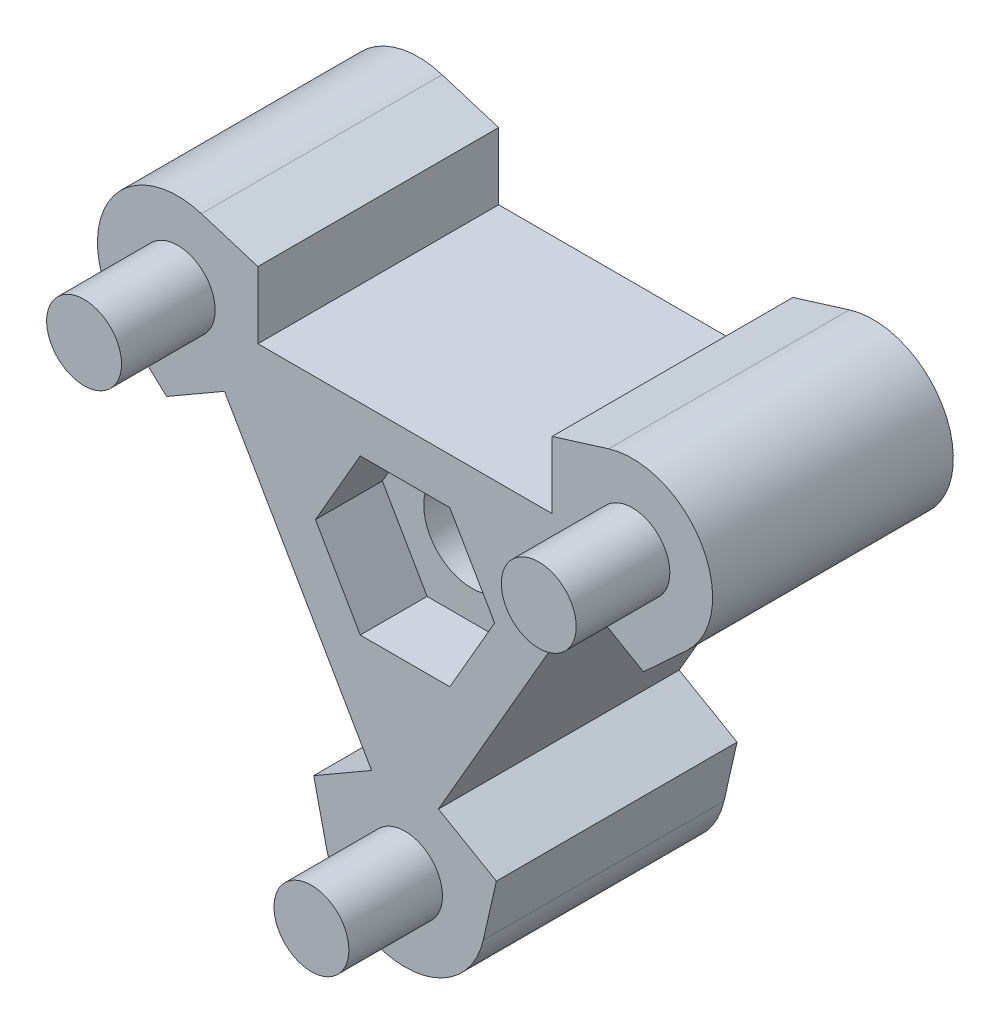
SolidWorks part; units mm, degrees
ref_plane "正面" through (0, 0, 0) normal (0, 0, 1) x (1, 0, 0)
ref_plane "平面" through (0, 0, 0) normal (0, 1, 0) x (1, 0, 0)
ref_plane "右側面" through (0, 0, 0) normal (1, 0, 0) x (0, 0, -1)
sketch "ｽｹｯﾁ1" plane through (0, 0, 0) normal (0, 0, 1) x (1, 0, 0)
  line L0 (-6.75, 2.4537) -> (-8.9151, 1.2037)
  line L1 (0, -9.2376) -> (8, 4.6188) construction
  line L2 (8, 4.6188) -> (-8, 4.6188) construction
  line L3 (-8, 4.6188) -> (0, -9.2376) construction
  line L4 (8.5, 4.9075) -> (-8.5, 4.9075) construction
  line L5 (-8.5, 4.9075) -> (0, -9.815) construction
  line L6 (0, -9.815) -> (8.5, 4.9075) construction
  line L7 (-8.9151, 1.2037) -> (-10.5379, 2.7059)
  line L8 (-1.25, -7.0725) -> (-3.4151, -8.3225)
  line L9 (-3.4151, -8.3225) -> (-2.9256, -10.479)
  line L10 (-8.9151, 1.2037) -> (-3.4151, -8.3225) construction
  line L11 (5.5, 7.1188) -> (7.6123, 7.7731)
  line L12 (5.5, 4.6188) -> (5.5, 7.1188)
  line L13 (-5.5, 7.1188) -> (-7.6123, 7.7731)
  line L14 (-5.5, 4.6188) -> (-5.5, 7.1188)
  line L15 (3.4151, -8.3225) -> (2.9256, -10.479)
  line L16 (1.25, -7.0725) -> (3.4151, -8.3225)
  line L17 (8.9151, 1.2037) -> (10.5379, 2.7059)
  line L18 (6.75, 2.4537) -> (8.9151, 1.2037)
  line L19 (-6.75, 2.4537) -> (-1.25, -7.0725)
  line L20 (1.25, -7.0725) -> (6.75, 2.4537)
  line L21 (5.5, 4.6188) -> (-5.5, 4.6188)
  circle A0 centre (0, 0) radius 4.6188 construction
  circle A1 centre (0, 0) radius 4.9075 construction
  arc A2 (-7, 2.3094) -> (-6.757, 2.4658) centre (-8.5, 4.9075) ccw
  arc A3 (1.5, -7.2169) -> (1.243, -7.0846) centre (0, -9.815) ccw
  arc A4 (5.5, 4.9075) -> (5.5139, 4.6188) centre (8.5, 4.9075) ccw
  arc A5 (-7.6123, 7.7731) -> (-10.5379, 2.7059) centre (-8.5, 4.9075) ccw
  arc A6 (10.5379, 2.7059) -> (7.6123, 7.7731) centre (8.5, 4.9075) ccw
  arc A7 (-2.9256, -10.479) -> (2.9256, -10.479) centre (0, -9.815) ccw
  arc A8 (-5.5139, 4.6188) -> (-5.5, 4.9075) centre (-8.5, 4.9075) ccw
  arc A9 (6.757, 2.4658) -> (7, 2.3094) centre (8.5, 4.9075) ccw
  arc A10 (-1.243, -7.0846) -> (-1.5, -7.2169) centre (0, -9.815) ccw
  point P19 (-4, -2.3094)
  point P34 (0, 0)
  dimension "D3" = 6
  dimension "D1" = 16
  dimension "D2" = 17
  dimension "D4" = 11
  dimension "D5" = 5.5
  dimension "D6" = 2.5
  dimension "D7" = 3
extrude "ﾎﾞｽ - 押し出し1" add sketch "ｽｹｯﾁ1" along normal blind 4
sketch "ｽｹｯﾁ2" plane through (0, 0, 4) normal (0, 0, 1) x (1, 0, 0)
  circle A0 centre (-8.5, 4.9075) radius 1.4
  circle A1 centre (0, -9.815) radius 1.4
  circle A2 centre (8.5, 4.9075) radius 1.4
  dimension "D1" = 2.8
extrude "ﾎﾞｽ - 押し出し2" add sketch "ｽｹｯﾁ2" along normal blind 3.5
sketch "ｽｹｯﾁ4" plane through (0, 0, 4) normal (0, 0, 1) x (1, 0, 0)
  line L1 (-1.6743, -2.9) -> (1.6743, -2.9)
  line L2 (1.6743, -2.9) -> (3.3486, 0)
  line L3 (3.3486, 0) -> (1.6743, 2.9)
  line L4 (1.6743, 2.9) -> (-1.6743, 2.9)
  line L5 (-1.6743, 2.9) -> (-3.3486, 0)
  line L6 (-3.3486, 0) -> (-1.6743, -2.9)
  circle A0 centre (0, 0) radius 2.9 construction
  dimension "D1" = 5.8
extrude "ｶｯﾄ - 押し出し1" cut sketch "ｽｹｯﾁ4" against normal blind 2.5
sketch "ｽｹｯﾁ6" plane through (0, 0, 0) normal (0, 0, -1) x (-1, 0, 0)
  circle A0 centre (0, 0) radius 1.8
  dimension "D1" = 3.6
extrude "ｶｯﾄ - 押し出し2" cut sketch "ｽｹｯﾁ6" against normal through all
sketch "ｽｹｯﾁ7" plane through (0, 0, 0) normal (0, 0, -1) x (-1, 0, 0)
  line L15 (-8.9151, 1.2037) -> (-6.75, 2.4537)
  line L16 (-6.75, 2.4537) -> (-1.25, -7.0725)
  line L17 (-1.25, -7.0725) -> (-3.4151, -8.3225)
  line L18 (-3.4151, -8.3225) -> (-2.9256, -10.479)
  line L19 (2.9256, -10.479) -> (3.4151, -8.3225)
  line L20 (3.4151, -8.3225) -> (1.25, -7.0725)
  line L21 (1.25, -7.0725) -> (6.75, 2.4537)
  line L22 (6.75, 2.4537) -> (8.9151, 1.2037)
  line L23 (8.9151, 1.2037) -> (10.5379, 2.7059)
  line L24 (7.6123, 7.7731) -> (5.5, 7.1188)
  line L25 (5.5, 7.1188) -> (5.5, 4.6188)
  line L26 (5.5, 4.6188) -> (-5.5, 4.6188)
  line L27 (-5.5, 4.6188) -> (-5.5, 7.1188)
  line L28 (-5.5, 7.1188) -> (-7.6123, 7.7731)
  line L29 (-10.5379, 2.7059) -> (-8.9151, 1.2037)
  line L30 (-8.9151, 1.2037) -> (-6.75, 2.4537)
  line L31 (-6.75, 2.4537) -> (-1.25, -7.0725)
  line L32 (-1.25, -7.0725) -> (-3.4151, -8.3225)
  line L33 (-3.4151, -8.3225) -> (-2.9256, -10.479)
  line L34 (2.9256, -10.479) -> (3.4151, -8.3225)
  line L35 (3.4151, -8.3225) -> (1.25, -7.0725)
  line L36 (1.25, -7.0725) -> (6.75, 2.4537)
  line L37 (6.75, 2.4537) -> (8.9151, 1.2037)
  line L38 (8.9151, 1.2037) -> (10.5379, 2.7059)
  line L39 (7.6123, 7.7731) -> (5.5, 7.1188)
  line L40 (5.5, 7.1188) -> (5.5, 4.6188)
  line L41 (5.5, 4.6188) -> (-5.5, 4.6188)
  line L42 (-5.5, 4.6188) -> (-5.5, 7.1188)
  line L43 (-5.5, 7.1188) -> (-7.6123, 7.7731)
  line L44 (-10.5379, 2.7059) -> (-8.9151, 1.2037)
  circle A0 centre (0, 0) radius 1.8 construction
  circle A1 centre (0, 0) radius 1.8
  arc A3 (-2.9256, -10.479) -> (2.9256, -10.479) centre (0, -9.815) ccw
  arc A4 (10.5379, 2.7059) -> (7.6123, 7.7731) centre (8.5, 4.9075) ccw
  arc A5 (-7.6123, 7.7731) -> (-10.5379, 2.7059) centre (-8.5, 4.9075) ccw
  arc A6 (-2.9256, -10.479) -> (2.9256, -10.479) centre (0, -9.815) ccw
  arc A7 (10.5379, 2.7059) -> (7.6123, 7.7731) centre (8.5, 4.9075) ccw
  arc A8 (-7.6123, 7.7731) -> (-10.5379, 2.7059) centre (-8.5, 4.9075) ccw
  dimension "D1" = 0
extrude "ﾎﾞｽ - 押し出し3" add sketch "ｽｹｯﾁ7" along normal blind 5
equation "\"D5@ｽｹｯﾁ1\"=\"D4@ｽｹｯﾁ1\"/2"
